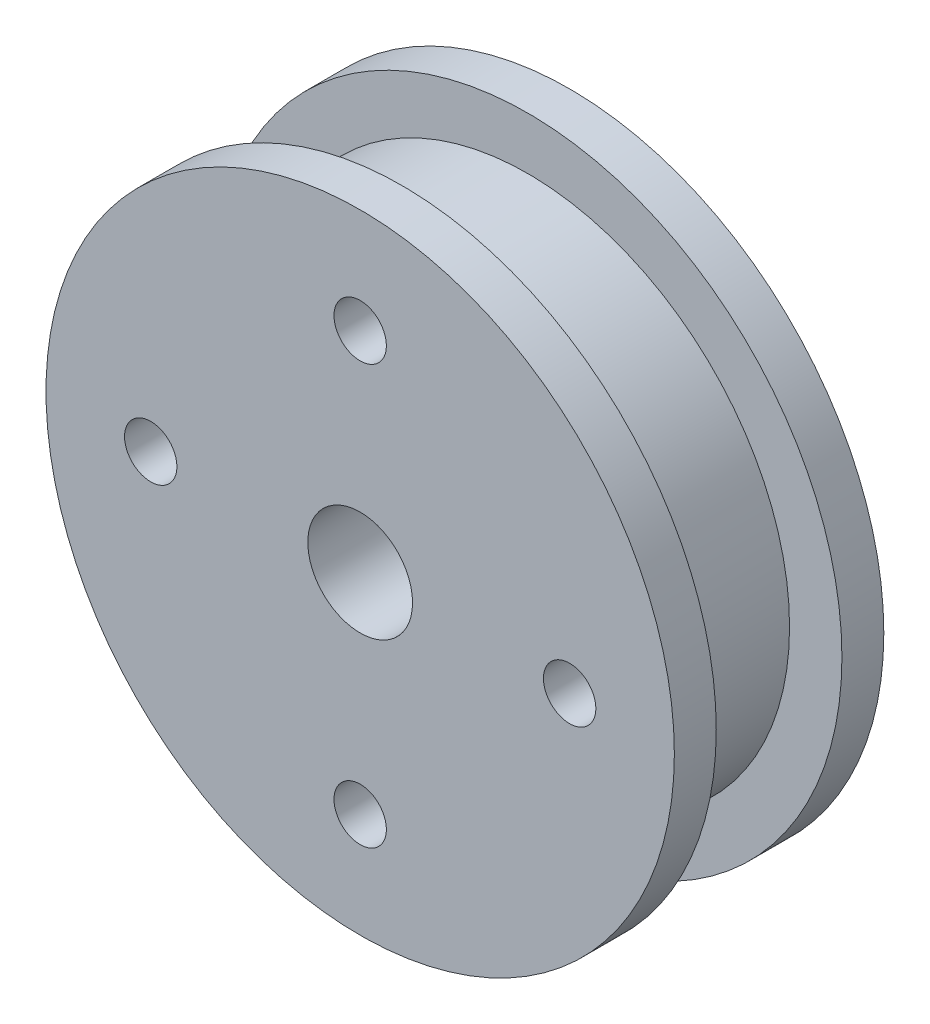
SolidWorks part; units mm, degrees
ref_plane "Front Plane" through (0, 0, 0) normal (0, 0, 1) x (1, 0, 0)
ref_plane "Top Plane" through (0, 0, 0) normal (0, 1, 0) x (1, 0, 0)
ref_plane "Right Plane" through (0, 0, 0) normal (1, 0, 0) x (0, 0, -1)
sketch "Sketch1" plane through (0, 0, 0) normal (0, 0, 1) x (1, 0, 0)
  circle A0 centre (0, 0) radius 19.05
  dimension "D1" = 38.1
extrude "Boss-Extrude1" add sketch "Sketch1" along normal blind 2.54
sketch "Sketch2" plane through (0, 0, 2.54) normal (0, 0, 1) x (1, 0, 0)
  circle A0 centre (0, 0) radius 15.875
  dimension "D1" = 31.75
extrude "Boss-Extrude2" add sketch "Sketch2" along normal blind 7.62
ref_plane "Plane1" through (0, 0, 6.35) normal (0, 0, 1) x (1, 0, 0)
mirror "Mirror1" about plane through (0, 0, 6.35) normal (0, 0, 1) of "Boss-Extrude1"
sketch "Sketch4" plane through (0, 0, 12.7) normal (0, 0, 1) x (1, 0, 0)
  circle A0 centre (0, 0) radius 3.175
  dimension "D1" = 6.35
extrude "Cut-Extrude1" cut sketch "Sketch4" against normal up to next
sketch "Sketch5" plane through (0, 0, 0) normal (0, 0, -1) x (-1, 0, 0)
  line L0 (0, 12.7) -> (0, -12.7) construction
  line L1 (-12.7, 0) -> (12.7, 0) construction
  circle A0 centre (0, 12.7) radius 1.5875
  circle A1 centre (12.7, 0) radius 1.5875
  circle A2 centre (0, -12.7) radius 1.5875
  circle A3 centre (-12.7, 0) radius 1.5875
  point P4 (0, 0)
  point P5 (0, 0)
  dimension "D2" = 3.175
  dimension "D1" = 12.7
extrude "Cut-Extrude2" cut sketch "Sketch5" against normal up to next
